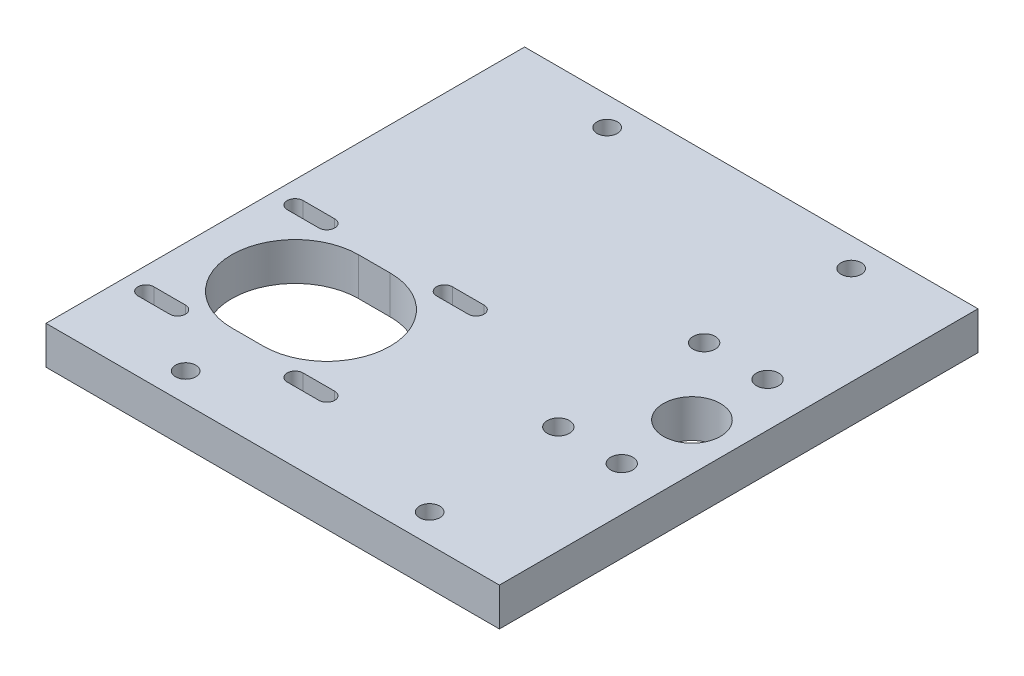
SolidWorks part; units mm, degrees
ref_plane "Front Plane" through (0, 0, 0) normal (0, 0, 1) x (1, 0, 0)
ref_plane "Top Plane" through (0, 0, 0) normal (0, 1, 0) x (1, 0, 0)
ref_plane "Right Plane" through (0, 0, 0) normal (1, 0, 0) x (0, 0, -1)
sketch "Sketch1" plane through (0, 0, 0) normal (0, 1, 0) x (1, 0, 0)
  line L1 (-73.5, -75.5) -> (73.5, -75.5)
  line L2 (-73.5, -75.5) -> (-73.5, 75.5)
  line L3 (-73.5, 75.5) -> (73.5, 75.5)
  line L4 (73.5, -75.5) -> (73.5, 75.5)
  line L5 (-73.5, -75.5) -> (73.5, 75.5) construction
  line L6 (-73.5, 75.5) -> (73.5, -75.5) construction
  point P0 (0, 0)
  dimension "D1" = 147
  dimension "D2" = 151
extrude "Boss-Extrude1" add sketch "Sketch1" along normal blind 12
sketch "Sketch2" plane through (0, 12, 0) normal (0, 1, 0) x (1, 0, 0)
  line L0 (0, 0) -> (73.5, 0) construction
  line L1 (73.5, -75.5) -> (73.5, 75.5) construction
  line L2 (40.65, 23) -> (40.65, -23) construction
  line L3 (40.65, -23) -> (20.65, -23) construction
  line L4 (20.65, -23) -> (20.65, 23) construction
  line L5 (20.65, 23) -> (40.65, 23) construction
  circle A0 centre (39.8, 0) radius 9
  circle A1 centre (20.65, -23) radius 3.5
  circle A2 centre (40.65, -23) radius 3.5
  circle A3 centre (40.65, 23) radius 3.5
  circle A4 centre (20.65, 23) radius 3.5
  dimension "D1" = 18
  dimension "D2" = 0.85
extrude "Cut-Extrude1" cut sketch "Sketch2" against normal through all
sketch "Sketch3" plane through (0, 0, 0) normal (0, -1, 0) x (1, 0, 0)
  line L0 (73.5, 0) -> (-73.5, 0) construction
  line L1 (73.5, 75.5) -> (73.5, -75.5) construction
  line L2 (-73.5, -75.5) -> (-73.5, 75.5) construction
  line L4 (-7.1, -28.2) -> (-63.5, -28.2)
  line L5 (-7.1, -28.2) -> (-7.1, 28.2)
  line L6 (-7.1, 28.2) -> (-63.5, 28.2)
  line L7 (-63.5, -28.2) -> (-63.5, 28.2)
  line L8 (-7.1, -28.2) -> (-63.5, 28.2) construction
  line L9 (-7.1, 28.2) -> (-63.5, -28.2) construction
  point P6 (-35.3, 0)
  dimension "D1" = 56.4
  dimension "D2" = 56.4
  dimension "D3" = 10
extrude "Cut-Extrude2" [suppressed] cut sketch "Sketch3" against normal through all
sketch "Sketch6" plane through (0, 12, 0) normal (0, 1, 0) x (1, 0, 0)
  line L1 (-73.5, 75.5) -> (-88.5, 75.5)
  line L2 (-73.5, 75.5) -> (-73.5, -75.5)
  line L3 (-73.5, -75.5) -> (-88.5, -75.5)
  line L4 (-88.5, 75.5) -> (-88.5, -75.5)
  dimension "D1" = 15
extrude "Boss-Extrude2" add sketch "Sketch6" against normal blind 12
sketch "Sketch4" plane through (0, 0, 0) normal (0, -1, 0) x (1, 0, 0)
  line L0 (7.1012, 27.45) -> (-67.8988, 27.45) construction
  line L1 (-34.4, 3.9) -> (-81.5, 3.9) construction
  line L2 (-34.4, 3.9) -> (-34.4, 51) construction
  line L3 (-34.4, 51) -> (-81.5, 51) construction
  line L4 (-81.5, 3.9) -> (-81.5, 51) construction
  line L5 (-34.4, 3.9) -> (-81.5, 51) construction
  line L6 (-34.4, 51) -> (-81.5, 3.9) construction
  line L8 (-71.5, 53.5) -> (-81.5, 53.5)
  line L9 (-71.5, 48.5) -> (-81.5, 48.5)
  line L10 (-71.5, 6.4) -> (-81.5, 6.4)
  line L11 (-71.5, 1.4) -> (-81.5, 1.4)
  line L12 (-57.95, 27.45) -> (-57.95, 51) construction
  line L13 (-57.95, 47.45) -> (-47.95, 47.45)
  line L14 (-57.95, 7.45) -> (-47.95, 7.45)
  line L15 (-52.95, 47.45) -> (-52.95, 11.4883) construction
  line L16 (-24.4, 3.9) -> (-24.4, 51) construction
  line L17 (-34.4, 1.4) -> (-24.4, 1.4)
  line L18 (-34.4, 6.4) -> (-24.4, 6.4)
  line L19 (-34.4, 48.5) -> (-24.4, 48.5)
  line L20 (-34.4, 53.5) -> (-24.4, 53.5)
  line L21 (-88.5, 75.5) -> (73.5, 75.5) construction
  line L23 (-88.5, -75.5) -> (-88.5, 75.5) construction
  circle A0 centre (-57.95, 27.45) radius 20 construction
  circle A1 centre (-81.5, 51) radius 2.5 construction
  circle A2 centre (-71.5, 3.9) radius 2.5 construction
  circle A3 centre (-81.5, 3.9) radius 2.5 construction
  arc A4 (-71.5, 1.4) -> (-71.5, 6.4) centre (-71.5, 3.9) ccw
  circle A5 centre (-71.5, 51) radius 2.5 construction
  arc A6 (-81.5, 53.5) -> (-81.5, 48.5) centre (-81.5, 51) ccw
  arc A7 (-71.5, 53.5) -> (-71.5, 48.5) centre (-71.5, 51) cw
  arc A8 (-81.5, 1.4) -> (-81.5, 6.4) centre (-81.5, 3.9) cw
  arc A9 (-57.95, 47.45) -> (-57.95, 7.45) centre (-57.95, 27.45) ccw
  arc A10 (-47.95, 47.45) -> (-47.95, 7.45) centre (-47.95, 27.45) cw
  circle A11 centre (-34.4, 51) radius 2.5 construction
  circle A12 centre (-24.4, 3.9) radius 2.5 construction
  circle A13 centre (-34.4, 3.9) radius 2.5 construction
  circle A14 centre (-24.4, 51) radius 2.5 construction
  arc A15 (-24.4, 1.4) -> (-24.4, 6.4) centre (-24.4, 3.9) ccw
  arc A16 (-34.4, 53.5) -> (-34.4, 48.5) centre (-34.4, 51) ccw
  arc A17 (-24.4, 53.5) -> (-24.4, 48.5) centre (-24.4, 51) cw
  arc A18 (-34.4, 1.4) -> (-34.4, 6.4) centre (-34.4, 3.9) cw
  point P50 (0, 0)
  point P51 (0, 0)
  dimension "D1" = 40
  dimension "D4" = 5
  dimension "D5" = 7
  dimension "D6" = 22
  dimension "D2" = 47.1
  dimension "D3" = 47.1
  dimension "D7" = 10
extrude "Cut-Extrude3" cut sketch "Sketch4" against normal through all
sketch "Sketch5" plane through (0, 12, 0) normal (0, 1, 0) x (1, 0, 0)
  line L0 (-88.5, -75.5) -> (73.5, -75.5) construction
  line L1 (73.5, 75.5) -> (54.55, 75.5)
  line L2 (73.5, 75.5) -> (73.5, -75.5)
  line L3 (73.5, -75.5) -> (54.55, -75.5)
  line L4 (54.55, 75.5) -> (54.55, -75.5)
  dimension "D1" = 18.95
extrude "Cut-Extrude4" cut sketch "Sketch5" against normal through all
sketch "Sketch7" plane through (0, 12, 0) normal (0, 1, 0) x (1, 0, 0)
  line L0 (-88.5, -66.5) -> (54.55, -66.5) construction
  line L1 (-88.5, 75.5) -> (-88.5, -75.5) construction
  line L2 (54.55, 75.5) -> (54.55, -75.5) construction
  line L3 (-88.5, -75.5) -> (54.55, -75.5) construction
  line L4 (0, 0) -> (-14.1048, 0) construction
  line L5 (-88.5, 66.5) -> (54.55, 66.5) construction
  circle A0 centre (23.55, -66.5) radius 3.2
  circle A1 centre (-53.45, -66.5) radius 3.2
  circle A2 centre (-53.45, 66.5) radius 3.2
  circle A3 centre (23.55, 66.5) radius 3.2
  dimension "D2" = 31
  dimension "D3" = 108
  dimension "D1" = 9
extrude "Cut-Extrude5" cut sketch "Sketch7" against normal through all
